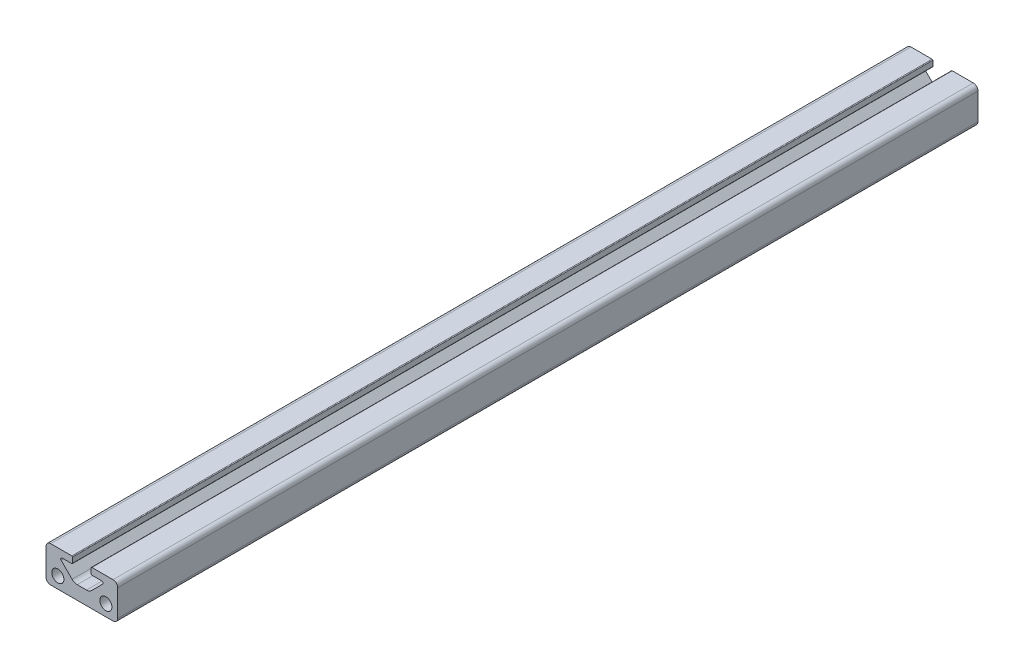
SolidWorks part; units mm, degrees
other "Imported1" parameters "D1"=304.8, "Length"=6096
ref_plane "Front" through (0, 0, 0) normal (0, 0, 1) x (1, 0, 0)
ref_plane "Top" through (0, 0, 0) normal (0, 1, 0) x (1, 0, 0)
ref_plane "Right" through (0, 0, 0) normal (1, 0, 0) x (0, 0, -1)
sketch "Sketch1" plane through (0, 0, 0) normal (0, 0, 1) x (1, 0, 0)
  line L0 (-3.302, 12.7) -> (3.302, 12.7) construction
  line L1 (-7.493, 9.8209) -> (7.493, 9.8209) construction
  line L2 (-11.049, 12.7) -> (-3.302, 12.7)
  line L3 (3.302, 12.7) -> (11.049, 12.7)
  line L4 (11.049, 0) -> (-11.049, 0)
  line L5 (-8.509, 4.064) -> (8.509, 4.064) construction
  line L6 (-3.302, 12.7) -> (-3.302, 10.3289)
  line L7 (3.302, 12.7) -> (3.302, 10.3289)
  line L28 (-12.7, 11.049) -> (-12.7, 1.651)
  line L32 (12.7, 1.651) -> (12.7, 11.049)
  line L35 (3.302, 10.3289) -> (6.985, 10.3289)
  line L36 (7.3442, 9.4617) -> (3.4525, 5.5699)
  line L37 (1.6565, 4.826) -> (-1.6565, 4.826)
  line L38 (-3.4525, 5.5699) -> (-7.3442, 9.4617)
  line L39 (-6.985, 10.3289) -> (-3.302, 10.3289)
  circle A0 centre (-8.509, 4.064) radius 2.1463
  circle A1 centre (8.509, 4.064) radius 2.1463
  arc A36 (-12.7, 1.651) -> (-11.049, 0) centre (-11.049, 1.651) ccw
  arc A41 (11.049, 0) -> (12.7, 1.651) centre (11.049, 1.651) ccw
  arc A42 (12.7, 11.049) -> (11.049, 12.7) centre (11.049, 11.049) ccw
  arc A46 (7.3442, 9.4617) -> (6.985, 10.3289) centre (6.985, 9.8209) ccw
  arc A47 (1.6565, 4.826) -> (3.4525, 5.5699) centre (1.6565, 7.366) ccw
  arc A48 (-3.4525, 5.5699) -> (-1.6565, 4.826) centre (-1.6565, 7.366) ccw
  arc A49 (-6.985, 10.3289) -> (-7.3442, 9.4617) centre (-6.985, 9.8209) ccw
  arc A53 (-11.049, 12.7) -> (-12.7, 11.049) centre (-11.049, 11.049) ccw
  point P5 (0, 4.064)
  point P8 (0, 0)
  point P10 (0, 4.826)
  point P11 (0, 9.8209)
  point P13 (0, 12.7)
  dimension "D6" = 1.651
  dimension "D7" = 0.508
  dimension "D8" = 8.636
  dimension "D9" = 4.2926
  dimension "D12" = 2.54
  dimension "D1" = 6.604
  dimension "D2" = 14.986
  dimension "D3" = 17.018
  dimension "D4" = 25.4
  dimension "D5" = 12.7
  dimension "D10" = 7.874
  dimension "D11" = 2.3711
  dimension "D13" = 45
sketch "Sketch2" plane through (0, 0, 0) normal (1, 0, 0) x (0, 0, -1)
  line L0 (3048, 0) -> (-3048, 0) construction
  point P4 (0, 0)
sketch "Sketch3" plane through (0, 0, 0) normal (0, 0, 1) x (1, 0, 0)
  line L0 (-11.049, 12.7) -> (-3.302, 12.7) construction
  line L1 (-3.302, 12.7) -> (-3.302, 10.3289) construction
  line L2 (-6.985, 10.3289) -> (-3.302, 10.3289) construction
  line L3 (-3.4525, 5.5699) -> (-7.3442, 9.4617) construction
  line L4 (1.6565, 4.826) -> (-1.6565, 4.826) construction
  line L5 (7.3442, 9.4617) -> (3.4525, 5.5699) construction
  line L6 (3.302, 10.3289) -> (6.985, 10.3289) construction
  line L7 (3.302, 12.7) -> (3.302, 10.3289) construction
  line L8 (3.302, 12.7) -> (11.049, 12.7) construction
  line L9 (12.7, 1.651) -> (12.7, 11.049) construction
  line L10 (11.049, 0) -> (-11.049, 0) construction
  line L11 (-12.7, 11.049) -> (-12.7, 1.651) construction
  line L12 (-11.049, 12.7) -> (-3.302, 12.7)
  line L13 (-3.302, 12.7) -> (-3.302, 10.3289)
  line L14 (-6.985, 10.3289) -> (-3.302, 10.3289)
  line L15 (-3.4525, 5.5699) -> (-7.3442, 9.4617)
  line L16 (1.6565, 4.826) -> (-1.6565, 4.826)
  line L17 (7.3442, 9.4617) -> (3.4525, 5.5699)
  line L18 (3.302, 10.3289) -> (6.985, 10.3289)
  line L19 (3.302, 12.7) -> (3.302, 10.3289)
  line L20 (3.302, 12.7) -> (11.049, 12.7)
  line L21 (12.7, 1.651) -> (12.7, 11.049)
  line L22 (11.049, 0) -> (-11.049, 0)
  line L23 (-12.7, 11.049) -> (-12.7, 1.651)
  circle A0 centre (8.509, 4.064) radius 2.1463 construction
  circle A1 centre (-8.509, 4.064) radius 2.1463 construction
  arc A2 (-6.985, 10.3289) -> (-7.3442, 9.4617) centre (-6.985, 9.8209) ccw construction
  arc A3 (-3.4525, 5.5699) -> (-1.6565, 4.826) centre (-1.6565, 7.366) ccw construction
  arc A4 (1.6565, 4.826) -> (3.4525, 5.5699) centre (1.6565, 7.366) ccw construction
  arc A5 (7.3442, 9.4617) -> (6.985, 10.3289) centre (6.985, 9.8209) ccw construction
  arc A6 (12.7, 11.049) -> (11.049, 12.7) centre (11.049, 11.049) ccw construction
  arc A7 (11.049, 0) -> (12.7, 1.651) centre (11.049, 1.651) ccw construction
  arc A8 (-12.7, 1.651) -> (-11.049, 0) centre (-11.049, 1.651) ccw construction
  arc A9 (-11.049, 12.7) -> (-12.7, 11.049) centre (-11.049, 11.049) ccw construction
  circle A10 centre (8.509, 4.064) radius 2.1463
  circle A11 centre (-8.509, 4.064) radius 2.1463
  arc A12 (-6.985, 10.3289) -> (-7.3442, 9.4617) centre (-6.985, 9.8209) ccw
  arc A13 (-3.4525, 5.5699) -> (-1.6565, 4.826) centre (-1.6565, 7.366) ccw
  arc A14 (1.6565, 4.826) -> (3.4525, 5.5699) centre (1.6565, 7.366) ccw
  arc A15 (7.3442, 9.4617) -> (6.985, 10.3289) centre (6.985, 9.8209) ccw
  arc A16 (12.7, 11.049) -> (11.049, 12.7) centre (11.049, 11.049) ccw
  arc A17 (11.049, 0) -> (12.7, 1.651) centre (11.049, 1.651) ccw
  arc A18 (-12.7, 1.651) -> (-11.049, 0) centre (-11.049, 1.651) ccw
  arc A19 (-11.049, 12.7) -> (-12.7, 11.049) centre (-11.049, 11.049) ccw
extrude "Boss-Extrude1" add sketch "Sketch3" along normal mid plane 304.8
fillet "Fillet1" radius 0.254 4 edges at (3.302, 10.3289, 0) (3.302, 12.7, 0) (-3.302, 10.3289, 0) (-3.302, 12.7, 0)
equation "\"D1@Boss-Extrude1\"=\"Length@Sketch2\""
